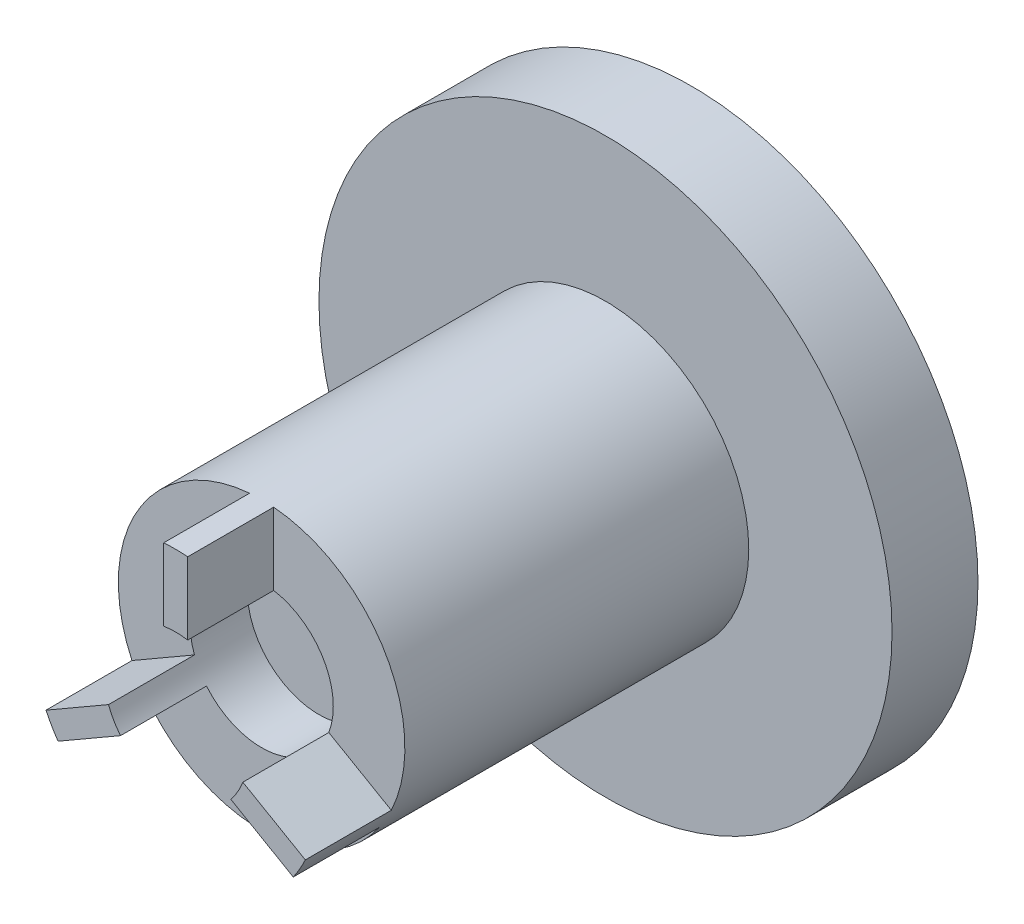
SolidWorks part; units mm, degrees
ref_plane "Front Plane" through (0, 0, 0) normal (0, 0, 1) x (1, 0, 0)
ref_plane "Top Plane" through (0, 0, 0) normal (0, 1, 0) x (1, 0, 0)
ref_plane "Right Plane" through (0, 0, 0) normal (1, 0, 0) x (0, 0, -1)
sketch "Sketch16" plane through (0, 0, 0) normal (0, 0, 1) x (1, 0, 0)
  circle A0 centre (0, 0) radius 10
  dimension "D1" = 20
extrude "Boss-Extrude4" add sketch "Sketch16" along normal mid plane 3
sketch "Sketch17" plane through (0, 0, 1.5) normal (0, 0, 1) x (1, 0, 0)
  circle A0 centre (0, 0) radius 5
  dimension "D1" = 10
extrude "Boss-Extrude5" add sketch "Sketch17" along normal blind 15
sketch "Sketch18" plane through (0, 0, 16.5) normal (0, 0, 1) x (1, 0, 0)
  circle A0 centre (0, 0) radius 2.5
  dimension "D1" = 5
extrude "Cut-Extrude4" cut sketch "Sketch18" against normal blind 5
sketch "Sketch19" plane through (0, 0, 16.5) normal (0, 0, 1) x (1, 0, 0)
  line L0 (0.4207, 2.4644) -> (0.4207, 4.9823)
  line L3 (-0.4207, 4.9823) -> (0.4207, 4.9823)
  line L5 (2.3445, -0.8679) -> (4.5251, -2.1268)
  line L6 (4.5251, -2.1268) -> (4.1044, -2.8554)
  line L7 (-0.4207, 2.4644) -> (-0.4207, 4.9823)
  line L8 (1.9239, -1.5965) -> (4.1044, -2.8554)
  line L9 (-1.9239, -1.5965) -> (-4.1044, -2.8554)
  line L10 (-4.1044, -2.8554) -> (-4.5251, -2.1268)
  line L11 (-2.3445, -0.8679) -> (-4.5251, -2.1268)
  circle A0 centre (0, 0) radius 5 construction
  circle A1 centre (0, 0) radius 2.5 construction
  circle A2 centre (0, 0) radius 2.5
  point P0 (0, 0)
  point P22 (0, 0)
  circle M6 centre (0, 0) radius 2.5
  circle M7 centre (0, 0) radius 5
  dimension "D1" = 3
extrude "Cut-Extrude7" cut sketch "Sketch19" against normal blind 3 contours L11 L7 M6 M7 | L5 L0 M6 M7 | L9 L8 M6 M7
